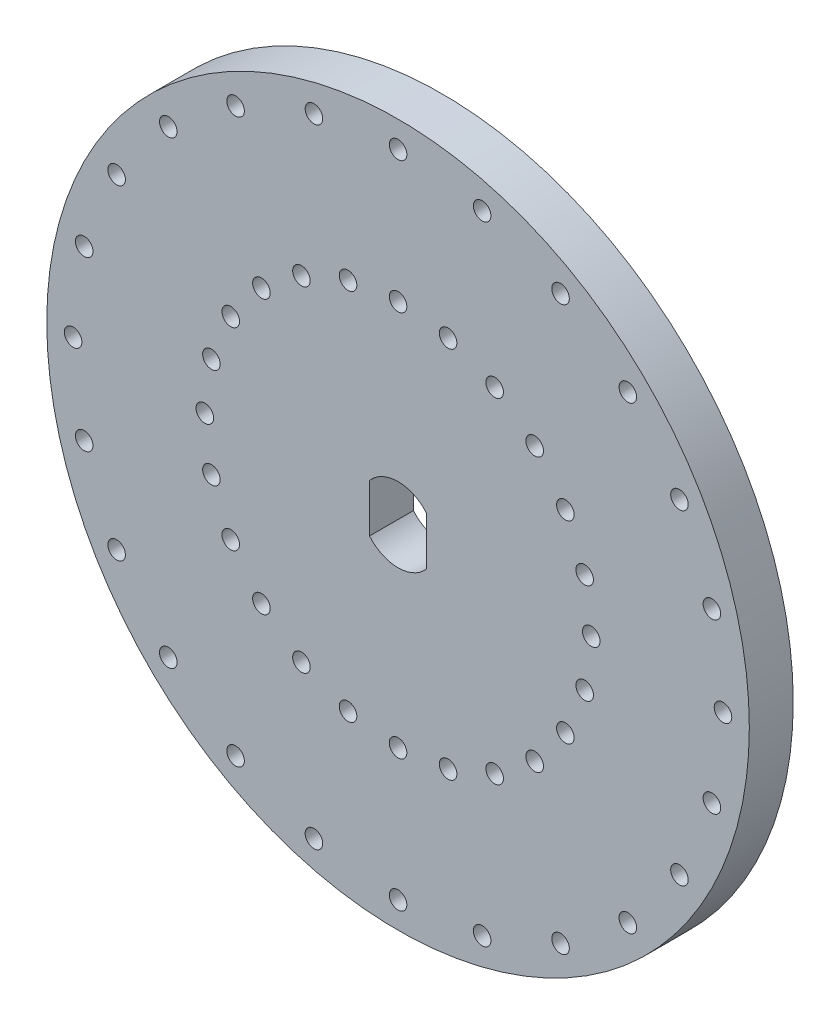
SolidWorks part; units mm, degrees
material "Pine"
ref_plane "Front Plane" through (0, 0, 0) normal (0, 0, 1) x (1, 0, 0)
ref_plane "Top Plane" through (0, 0, 0) normal (0, 1, 0) x (1, 0, 0)
ref_plane "Right Plane" through (0, 0, 0) normal (1, 0, 0) x (0, 0, -1)
sketch "Sketch1" plane through (0, 0, 0) normal (0, 0, 1) x (1, 0, 0)
  circle A0 centre (0, 0) radius 40
  dimension "D1" = 80
sketch "Sketch2" plane through (0, 0, 0) normal (0, 0, 1) x (1, 0, 0)
  line L0 (0, 0) -> (0, 40) construction
  circle A0 centre (0, 0) radius 40 construction
  circle A1 centre (0, 37) radius 1
  circle A2 centre (0, 22) radius 1
  circle A3 centre (5.694, 21.2504) radius 1
  circle A4 centre (9.5763, 35.7393) radius 1
  circle A5 centre (11, 19.0526) radius 1
  circle A6 centre (18.5, 32.0429) radius 1
  circle A7 centre (15.5563, 15.5563) radius 1
  circle A8 centre (26.163, 26.163) radius 1
  circle A9 centre (19.0526, 11) radius 1
  circle A10 centre (32.0429, 18.5) radius 1
  circle A11 centre (21.2504, 5.694) radius 1
  circle A12 centre (35.7393, 9.5763) radius 1
  circle A13 centre (22, 0) radius 1
  circle A14 centre (37, 0) radius 1
  circle A15 centre (21.2504, -5.694) radius 1
  circle A16 centre (35.7393, -9.5763) radius 1
  circle A17 centre (19.0526, -11) radius 1
  circle A18 centre (32.0429, -18.5) radius 1
  circle A19 centre (15.5563, -15.5563) radius 1
  circle A20 centre (26.163, -26.163) radius 1
  circle A21 centre (11, -19.0526) radius 1
  circle A22 centre (18.5, -32.0429) radius 1
  circle A23 centre (5.694, -21.2504) radius 1
  circle A24 centre (9.5763, -35.7393) radius 1
  circle A25 centre (0, -22) radius 1
  circle A26 centre (0, -37) radius 1
  circle A27 centre (-5.694, -21.2504) radius 1
  circle A28 centre (-9.5763, -35.7393) radius 1
  circle A29 centre (-11, -19.0526) radius 1
  circle A30 centre (-18.5, -32.0429) radius 1
  circle A31 centre (-15.5563, -15.5563) radius 1
  circle A32 centre (-26.163, -26.163) radius 1
  circle A33 centre (-19.0526, -11) radius 1
  circle A34 centre (-32.0429, -18.5) radius 1
  circle A35 centre (-21.2504, -5.694) radius 1
  circle A36 centre (-35.7393, -9.5763) radius 1
  circle A37 centre (-22, 0) radius 1
  circle A38 centre (-37, 0) radius 1
  circle A39 centre (-21.2504, 5.694) radius 1
  circle A40 centre (-35.7393, 9.5763) radius 1
  circle A41 centre (-19.0526, 11) radius 1
  circle A42 centre (-32.0429, 18.5) radius 1
  circle A43 centre (-15.5563, 15.5563) radius 1
  circle A44 centre (-26.163, 26.163) radius 1
  circle A45 centre (-11, 19.0526) radius 1
  circle A46 centre (-18.5, 32.0429) radius 1
  circle A47 centre (-5.694, 21.2504) radius 1
  circle A48 centre (-9.5763, 35.7393) radius 1
  point P104 (0, 0)
  dimension "D1" = 2
  dimension "D2" = 3
  dimension "D3" = 15
  dimension "D4" = 24
sketch "Sketch5" plane through (0, 0, 0) normal (0, 0, 1) x (1, 0, 0)
  line L0 (-3.25, 2.7386) -> (-3.25, -2.7386)
  line L1 (0, 4.25) -> (0, -4.25) construction
  line L2 (3.25, 2.7386) -> (3.25, -2.7386)
  arc A0 (-3.25, -2.7386) -> (3.25, -2.7386) centre (0, 0) ccw
  arc A1 (3.25, 2.7386) -> (-3.25, 2.7386) centre (0, 0) ccw
  dimension "D1" = 8.5
  dimension "D2" = 6.5
extrude "Boss-Extrude1" add sketch "Sketch1" along normal blind 5
extrude "Cut-Extrude1" cut sketch "Sketch2" along normal blind 5
extrude "Cut-Extrude2" cut sketch "Sketch5" along normal blind 5
